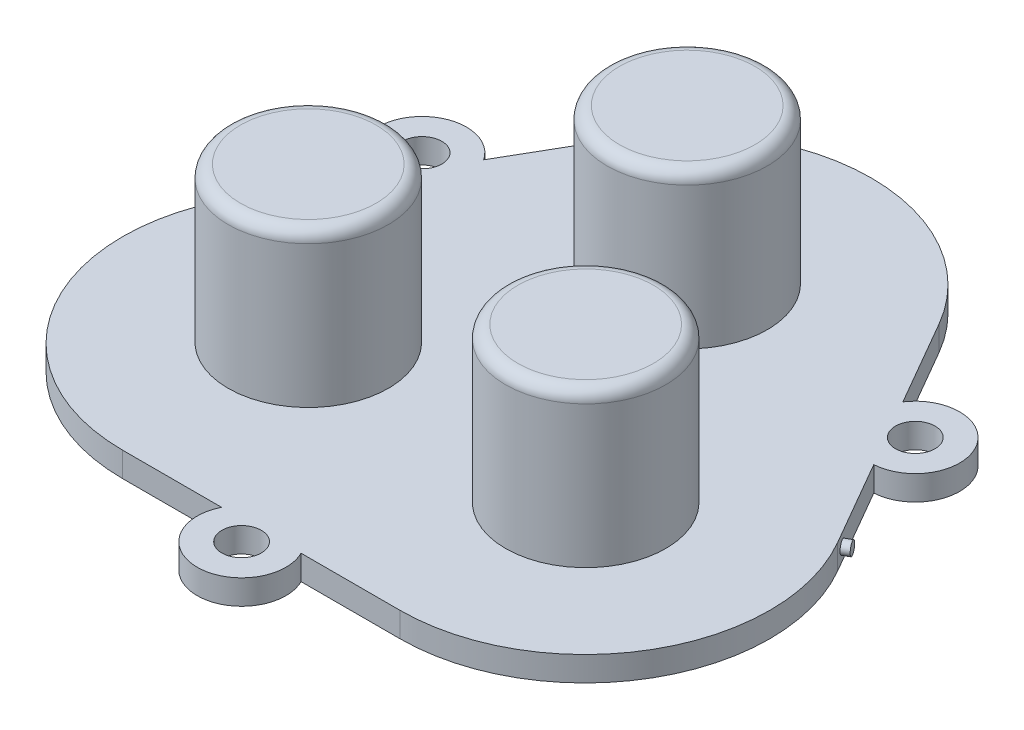
SolidWorks part; units mm, degrees
ref_plane "Front Plane" through (0, 0, 0) normal (0, 0, 1) x (1, 0, 0)
ref_plane "Top Plane" through (0, 0, 0) normal (0, 1, 0) x (1, 0, 0)
ref_plane "Right Plane" through (0, 0, 0) normal (1, 0, 0) x (0, 0, -1)
sketch "Sketch5" plane through (0, 0, 0) normal (0, 1, 0) x (1, 0, 0)
  line L3 (-11.25, -22.1428) -> (-3.2249, -22.1428)
  line L4 (3.2249, -22.1428) -> (11.25, -22.1428)
  line L5 (24.2404, 0.3572) -> (20.2278, 7.3072)
  line L6 (17.0029, 12.8928) -> (12.9904, 19.8428)
  line L7 (-12.9904, 19.8428) -> (-17.0029, 12.8928)
  line L8 (-20.2278, 7.3072) -> (-24.2404, 0.3572)
  arc A3 (-3.2249, -22.1428) -> (3.2249, -22.1428) centre (0, -23.7428) ccw
  arc A4 (11.25, -22.1428) -> (24.2404, 0.3572) centre (11.25, -7.1428) ccw
  arc A5 (20.2278, 7.3072) -> (17.0029, 12.8928) centre (20.001, 10.9) ccw
  arc A6 (12.9904, 19.8428) -> (-12.9904, 19.8428) centre (0, 12.3428) ccw
  arc A7 (-17.0029, 12.8928) -> (-20.2278, 7.3072) centre (-20.001, 10.9) ccw
  arc A8 (-24.2404, 0.3572) -> (-11.25, -22.1428) centre (-11.25, -7.1428) ccw
  circle A9 centre (20.001, 10.9) radius 1.6
  circle A10 centre (0, -23.7428) radius 1.6
  circle A11 centre (-20.001, 10.9) radius 1.6
extrude "Boss-Extrude2" add sketch "Sketch5" along normal blind 2
sketch "Sketch6" plane through (0, 0, 0) normal (0, 1, 0) x (1, 0, 0)
  circle A12 centre (-0.06, 12.4628) radius 6.5
  circle A13 centre (11.19, -7.0227) radius 6.5
  circle A14 centre (-11.31, -7.0227) radius 6.5
  dimension "D1" = 13
extrude "Boss-Extrude3" add sketch "Sketch6" along normal blind 14.5
fillet "Fillet1" radius 1 3 edges at (-11.31, 14.5, 13.5227) (11.19, 14.5, 13.5227) (-0.06, 14.5, -5.9628)
sketch "Sketch7" plane through (18.335, 0, -10.5857) normal (0.866, 0, -0.5) x (-0.5, 0, -0.866)
  circle A0 centre (-10.764, 1) radius 0.5
  dimension "D1" = 1
extrude "Boss-Extrude4" add sketch "Sketch7" along normal blind 0.6
